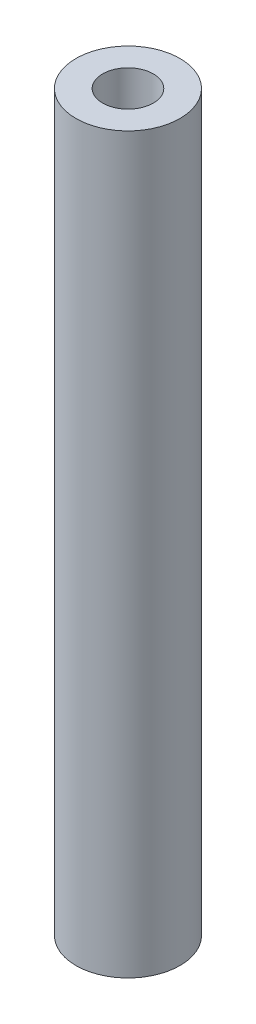
SolidWorks part; units mm, degrees
ref_plane "Front Plane" through (0, 0, 0) normal (0, 0, 1) x (1, 0, 0)
ref_plane "Top Plane" through (0, 0, 0) normal (0, 1, 0) x (1, 0, 0)
ref_plane "Right Plane" through (0, 0, 0) normal (1, 0, 0) x (0, 0, -1)
sketch "Sketch1" plane through (0, 0, 0) normal (0, 1, 0) x (1, 0, 0)
  circle A0 centre (0, 0) radius 1.9
  circle A1 centre (0, 0) radius 3.9
  dimension "D1" = 3.8
  dimension "D2" = 2
extrude "Boss-Extrude1" add sketch "Sketch1" along normal blind 55
